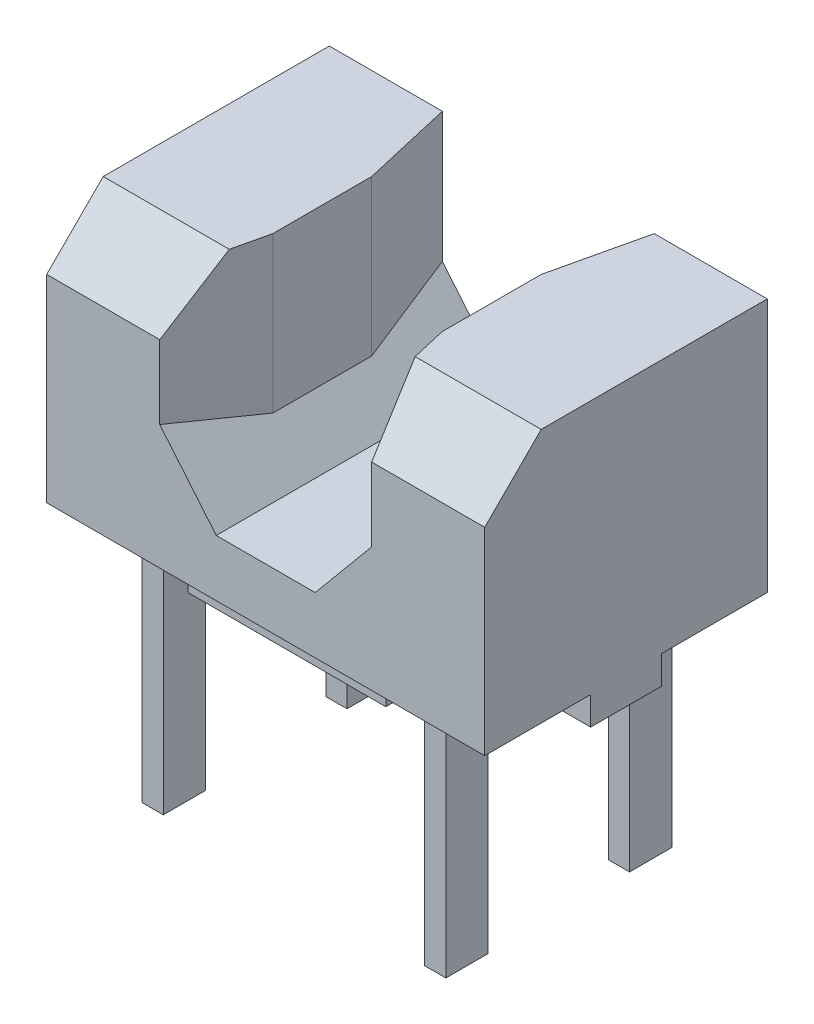
SolidWorks part; units mm, degrees
ref_plane "Front Plane" through (0, 0, 0) normal (0, 0, 1) x (1, 0, 0)
ref_plane "Top Plane" through (0, 0, 0) normal (0, 1, 0) x (1, 0, 0)
ref_plane "Right Plane" through (0, 0, 0) normal (1, 0, 0) x (0, 0, -1)
sketch "Sketch1" plane through (0, 0, 0) normal (0, 0, 1) x (1, 0, 0)
  line L0 (-0.75, 2) -> (-0.75, 1.08)
  line L1 (-1.55, 2) -> (-0.75, 2)
  line L2 (-1.55, 2) -> (-1.55, 0)
  line L3 (-1.55, 0) -> (1.55, 0)
  line L4 (1.55, 2) -> (1.55, 0)
  line L5 (-0.35, 0.6) -> (-0.75, 1.08)
  line L6 (-0.35, 0.6) -> (0.35, 0.6)
  line L7 (0.35, 0.6) -> (0.75, 1.08)
  line L8 (0.75, 1.08) -> (0.75, 2)
  line L9 (0.75, 2) -> (1.55, 2)
  point P6 (0.6, 0.9)
  dimension "D1" = 3.1
  dimension "D2" = 2
  dimension "D3" = 1.4
  dimension "D4" = 1.5
  dimension "D5" = 0.7
  dimension "D6" = 1.1
  dimension "D7" = 0.6
extrude "Boss-Extrude1" add sketch "Sketch1" along normal mid plane 2
sketch "Sketch2" plane through (0, 2, 0) normal (0, 1, 0) x (1, 0, 0)
  line L0 (0.75, 1) -> (0.6, 0.35)
  line L1 (0.6, 0.35) -> (0.6, -0.35)
  line L2 (0.6, -0.35) -> (0.75, -1)
  line L3 (0.75, -1) -> (0.75, 1)
  dimension "D1" = 0.6
  dimension "D2" = 0.7
extrude "Boss-Extrude2" add sketch "Sketch2" against normal up to next
mirror "Mirror1" about plane through (0, 0, 0) normal (1, 0, 0) of "Boss-Extrude2"
chamfer "Chamfer1" distance 0.4 angle 45 2 edges at (1.15, 2, 1) (-1.15, 2, 1)
sketch "Sketch3" plane through (0, 0, 0) normal (0, -1, 0) x (1, 0, 0)
  line L0 (-0.7, -0.25) -> (-1.55, -0.25)
  line L1 (-1.55, 1) -> (1.55, 1)
  line L2 (-1.55, 1) -> (-1.55, 0.25)
  line L3 (-1.55, -1) -> (1.55, -1)
  line L4 (1.55, 1) -> (1.55, 0.25)
  line L5 (1.55, -0.25) -> (0.7, -0.25)
  line L6 (-0.7, -0.25) -> (-0.7, -0.85)
  line L7 (1.55, 0.25) -> (0.7, 0.25)
  line L8 (-0.7, 0.25) -> (-1.55, 0.25)
  line L9 (-0.7, 0.85) -> (0.7, 0.85)
  line L10 (-0.7, 0.85) -> (-0.7, 0.25)
  line L11 (-0.7, -0.85) -> (0.7, -0.85)
  line L12 (0.7, 0.85) -> (0.7, 0.25)
  line L13 (0.7, -0.25) -> (0.7, -0.85)
  line L14 (1.55, -0.25) -> (1.55, -1)
  line L15 (-1.55, -0.25) -> (-1.55, -1)
  line L16 (-0.7, -0.85) -> (0.7, 0.85) construction
  line L17 (-0.7, -0.25) -> (0.7, 0.25) construction
  dimension "D1" = 1.7
  dimension "D2" = 1.4
  dimension "D3" = 0.5
extrude "Cut-Extrude1" cut sketch "Sketch3" against normal blind 0.2
sketch "Sketch4" plane through (0.6, 0, 0) normal (-1, 0, 0) x (0, 0, 1)
  line L0 (-1.1294, 1.65) -> (1.3748, 1.65) construction
  line L1 (-0.15, 1.85) -> (0.15, 1.85)
  line L2 (-0.15, 1.85) -> (-0.15, 1.35)
  line L3 (-0.15, 1.35) -> (0.15, 1.35)
  line L4 (0.15, 1.85) -> (0.15, 1.35)
  line L5 (0.6, 2) -> (-1, 2) construction
  line L6 (0, 0) -> (0, 1.35) construction
  dimension "D1" = 0.35
  dimension "D2" = 0.5
  dimension "D3" = 0.65
  dimension "D4" = 0.3
extrude "Cut-Extrude2" cut sketch "Sketch4" against normal blind 0.2
sketch "Sketch5" plane through (0, 0.2, 0) normal (0, -1, 0) x (1, 0, 0)
  line L0 (0.925, -0.65) -> (1.075, -0.65) construction
  line L1 (0.925, -0.5) -> (1.075, -0.5)
  line L2 (0.925, -0.5) -> (0.925, -0.8)
  line L3 (0.925, -0.8) -> (1.075, -0.8)
  line L4 (1.075, -0.5) -> (1.075, -0.8)
  line L5 (1, -0.5) -> (1, -0.8) construction
  dimension "D1" = 0.65
  dimension "D2" = 1
  dimension "D3" = 0.15
  dimension "D4" = 0.3
extrude "Boss-Extrude3" add sketch "Sketch5" along normal offset from surface (1.7 mm away) 1.5 up to face at (0, 0, 0) offset beyond the face yes
mirror "Mirror2" about plane through (0, 0, 0) normal (0, 0, 1) of "Boss-Extrude3"
mirror "Mirror3" about plane through (0, 0, 0) normal (1, 0, 0) of "Boss-Extrude3", "Mirror2"
